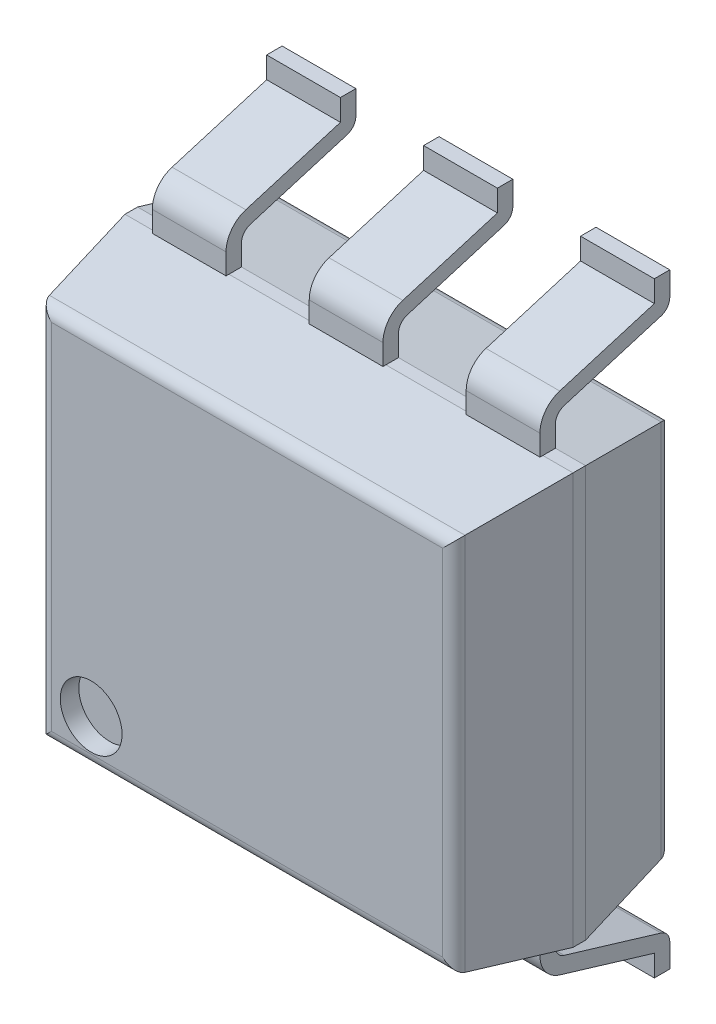
SolidWorks part; units mm, degrees
ref_plane "x/y" through (0, 0, 0) normal (0, 0, 1) x (1, 0, 0)
ref_plane "x/z" through (0, 0, 0) normal (0, 1, 0) x (1, 0, 0)
ref_plane "y/z" through (0, 0, 0) normal (1, 0, 0) x (0, 0, -1)
sketch "Sketch1" plane through (0, 0, 0) normal (0, 0, 1) x (1, 0, 0)
  line L0 (-0.635, 7.539) -> (6.615, 7.539)
  line L1 (-0.635, 7.539) -> (-0.635, 0.889)
  line L2 (6.615, 0.889) -> (-0.635, 0.889)
  line L3 (6.615, 0.889) -> (6.615, 7.539)
  dimension "D1" = 6.65
  dimension "D2" = 7.25
  dimension "D3" = 0.635
  dimension "D4" = 0.889
extrude "Base-Extrude" add sketch "Sketch1" along normal blind 3.5052
ref_plane "Plane1" through (0.45, 0, 0) normal (-1, 0, 0) x (0, 0, 1)
chamfer "Chamfer1" distance 1.651 angle 10 4 edges at (-0.635, 4.214, 3.5052) (2.99, 7.539, 3.5052) (6.615, 4.214, 3.5052) (2.99, 0.889, 3.5052)
chamfer "Chamfer2" distance 1.651 angle 10 4 edges at (2.99, 0.889, 0) (6.615, 4.214, 0) (2.99, 7.539, 0) (-0.635, 4.214, 0)
sketch "Sketch3" plane through (0.1189, 0.143, 3.5052) normal (0, 0, 1) x (1, 0, 0)
  circle A0 centre (0.3498, 1.7341) radius 0.5
  dimension "D1" = 1
extrude "Cut-Extrude1" cut sketch "Sketch3" against normal blind 0.3
ref_plane "Plane5" through (-0.5787, 0, 0) normal (-1, 0, 0) x (0, 0, 1)
sketch "Sketch4" plane through (0.45, 0, 0) normal (-1, 0, 0) x (0, 0, 1)
  line L0 (1.651, 0.889) -> (1.651, 0.5527)
  line L1 (0, 1.1801) -> (0, 7.2479) construction
  line L2 (1.5085, 0.3612) -> (-0.0575, -0.1093)
  line L3 (3.5052, 4.214) -> (0, 4.214) construction
  line L4 (3.5052, 1.1801) -> (3.5052, 7.2479) construction
  line L5 (-0.2, -0.3009) -> (-0.2, -0.686)
  line L6 (0, 7.2479) -> (0, 1.1801) construction
  arc A0 (-0.0575, -0.1093) -> (-0.2, -0.3009) centre (0, -0.3009) ccw
  arc A1 (1.5085, 0.3612) -> (1.651, 0.5527) centre (1.451, 0.5527) ccw
  point P18 (1.651, 0.404)
  dimension "D2" = 4.9
  dimension "D4" = 0.2
  dimension "D1" = 0.2
  dimension "D3" = 3.81
extrude "Boss-Extrude-Thin3" add sketch "Sketch4" along normal mid plane 1.1938 thin
pattern_linear "LPattern1" count 3 spacing 2.54 along (1, 0, 0) of "Boss-Extrude-Thin3"
ref_plane "Plane6" through (0, 4.214, 0) normal (0, -1, 0) x (1, 0, 0)
mirror "Mirror1" about plane through (0, 4.214, 0) normal (0, -1, 0) of "Boss-Extrude-Thin3", "LPattern1"
fillet "Скругление1" radius 0.2 8 edges at (-0.3439, 4.214, 0) (2.99, 7.2479, 0) (2.99, 1.1801, 0) (6.3239, 4.214, 0) (2.99, 7.2479, 3.5052) (2.99, 1.1801, 3.5052) (-0.3439, 4.214, 3.5052) (6.3239, 4.214, 3.5052)
sketch "Эскиз1" [suppressed] plane through (0, 0, 3.5052) normal (0, 0, 1) x (1, 0, 0)
  line L0 (1.6637, 7.3914) -> (1.6637, -0.6817) construction
  line L1 (-0.635, 7.3914) -> (3.9624, 7.3914) construction
  line L2 (0.1311, 9.2202) -> (-0.2032, 8.8859)
  line L3 (0.9906, 9.2202) -> (-0.2032, 9.2202) construction
  line L4 (-0.2032, 8.5515) -> (-0.2032, 9.2202) construction
  line L5 (-0.2032, 8.8859) -> (-0.2032, 9.2202)
  line L6 (-0.2032, 9.2202) -> (0.1311, 9.2202)
  line L7 (0.9906, 9.2202) -> (0.9906, 8.8859)
  line L8 (0.9906, 8.5515) -> (0.9906, 9.2202) construction
  line L9 (0.9906, 8.8859) -> (0.6563, 9.2202)
  line L10 (0.6563, 9.2202) -> (0.9906, 9.2202)
  line L12 (-0.2032, 7.3914) -> (0.1311, 7.3914)
  line L13 (-0.2032, 7.3914) -> (-0.2032, 8.1734)
  line L14 (-0.2032, 8.1734) -> (0.1311, 8.1734)
  line L15 (0.1311, 7.3914) -> (0.1311, 8.1734)
  line L16 (3.1963, 7.3914) -> (3.1963, 8.1734)
  line L17 (3.5306, 8.1734) -> (3.1963, 8.1734)
  line L18 (3.5306, 7.3914) -> (3.5306, 8.1734)
  line L19 (3.5306, 7.3914) -> (3.1963, 7.3914)
  line L20 (2.6711, 9.2202) -> (2.3368, 9.2202)
  line L21 (2.3368, 8.8859) -> (2.6711, 9.2202)
  line L22 (2.3368, 9.2202) -> (2.3368, 8.8859)
  line L23 (3.5306, 9.2202) -> (3.1963, 9.2202)
  line L24 (3.5306, 8.8859) -> (3.5306, 9.2202)
  line L25 (3.1963, 9.2202) -> (3.5306, 8.8859)
  line L26 (-0.635, 4.1402) -> (3.9624, 4.1402) construction
  line L27 (-0.635, 0.889) -> (-0.635, 7.3914) construction
  line L28 (3.9624, 7.3914) -> (3.9624, 0.889) construction
  line L29 (3.1963, -0.9398) -> (3.5306, -0.6055)
  line L30 (3.5306, -0.6055) -> (3.5306, -0.9398)
  line L31 (3.5306, -0.9398) -> (3.1963, -0.9398)
  line L32 (2.3368, -0.9398) -> (2.3368, -0.6055)
  line L33 (2.3368, -0.6055) -> (2.6711, -0.9398)
  line L34 (2.6711, -0.9398) -> (2.3368, -0.9398)
  line L35 (3.5306, 0.889) -> (3.1963, 0.889)
  line L36 (3.5306, 0.889) -> (3.5306, 0.107)
  line L37 (3.5306, 0.107) -> (3.1963, 0.107)
  line L38 (3.1963, 0.889) -> (3.1963, 0.107)
  line L39 (0.1311, 0.889) -> (0.1311, 0.107)
  line L40 (-0.2032, 0.107) -> (0.1311, 0.107)
  line L41 (-0.2032, 0.889) -> (-0.2032, 0.107)
  line L42 (-0.2032, 0.889) -> (0.1311, 0.889)
  line L43 (0.6563, -0.9398) -> (0.9906, -0.9398)
  line L44 (0.9906, -0.6055) -> (0.6563, -0.9398)
  line L45 (0.9906, -0.9398) -> (0.9906, -0.6055)
  line L46 (-0.2032, -0.9398) -> (0.1311, -0.9398)
  line L47 (-0.2032, -0.6055) -> (-0.2032, -0.9398)
  line L48 (0.1311, -0.9398) -> (-0.2032, -0.6055)
sketch "Эскиз2" [suppressed] plane through (0, 0, 3.5052) normal (0, 0, 1) x (1, 0, 0)
  line L0 (2.6655, 1.9049) -> (2.6655, 6.0765) construction
  text T0 "DIP-4S" font "Century Gothic" height 1
